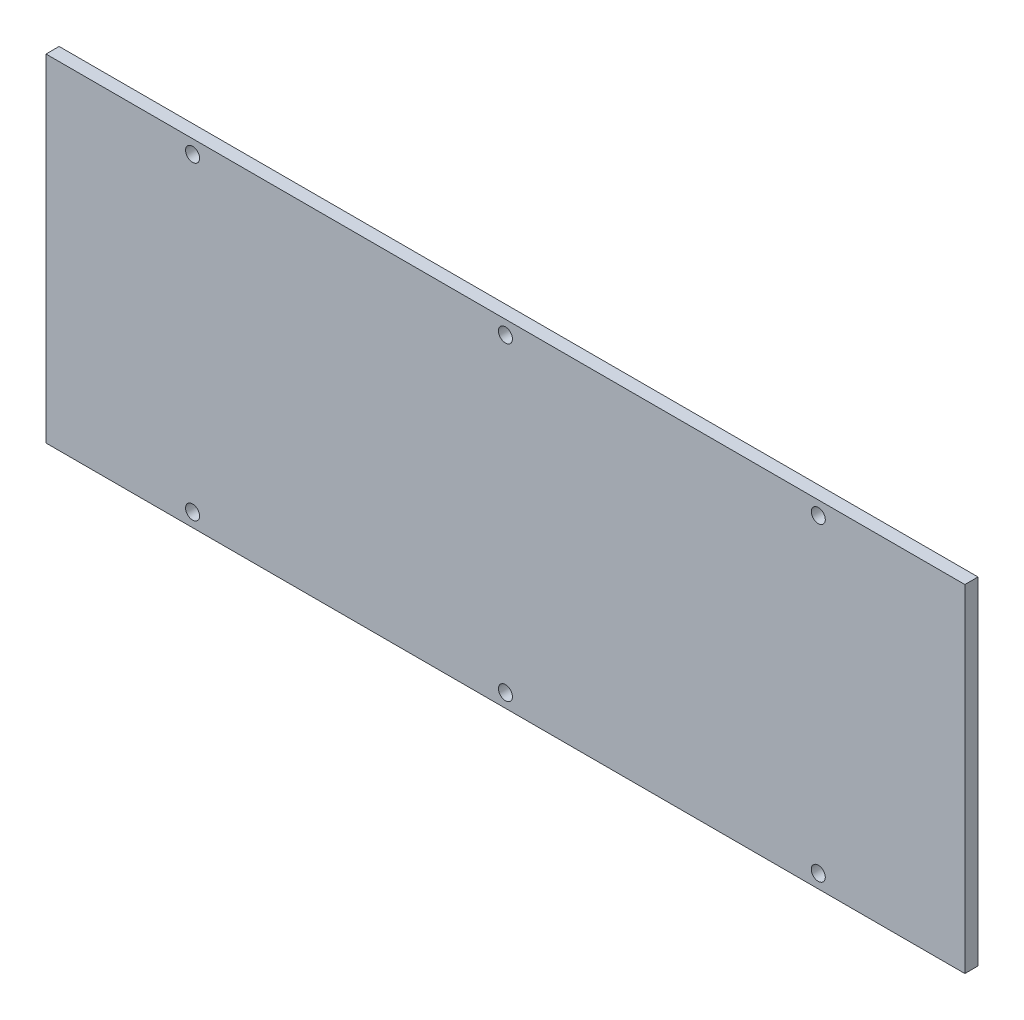
SolidWorks part; units mm, degrees
ref_plane "Alzado" through (0, 0, 0) normal (0, 0, 1) x (1, 0, 0)
ref_plane "Planta" through (0, 0, 0) normal (0, 1, 0) x (1, 0, 0)
ref_plane "Vista lateral" through (0, 0, 0) normal (1, 0, 0) x (0, 0, -1)
sketch "Croquis1" plane through (0, 0, 0) normal (0, 0, 1) x (1, 0, 0)
  line L0 (-105, 35.4) -> (-71.5, 35.4) construction
  line L1 (105, -38.5) -> (-105, -38.5)
  line L2 (105, -38.5) -> (105, 38.5)
  line L3 (105, 38.5) -> (-105, 38.5)
  line L4 (-105, -38.5) -> (-105, 38.5)
  line L5 (105, -38.5) -> (-105, 38.5) construction
  line L6 (105, 38.5) -> (-105, -38.5) construction
  line L7 (-71.5, 35.4) -> (0, 35.4) construction
  line L8 (0, 35.4) -> (71.5, 35.4) construction
  line L9 (71.5, 35.4) -> (105, 35.4) construction
  line L10 (-105, 0) -> (105, 0) construction
  circle A0 centre (0, 35.4) radius 1.6
  circle A1 centre (-71.5, 35.4) radius 1.6
  circle A2 centre (71.5, 35.4) radius 1.6
  circle A3 centre (71.5, -35.4) radius 1.6
  circle A4 centre (0, -35.4) radius 1.6
  circle A5 centre (-71.5, -35.4) radius 1.6
  point P0 (0, 0)
  dimension "D5" = 3.2
  dimension "D1" = 210
  dimension "D2" = 77
  dimension "D3" = 3.1
  dimension "D4" = 71.5
extrude "Saliente-Extruir1" add sketch "Croquis1" along normal blind 3
